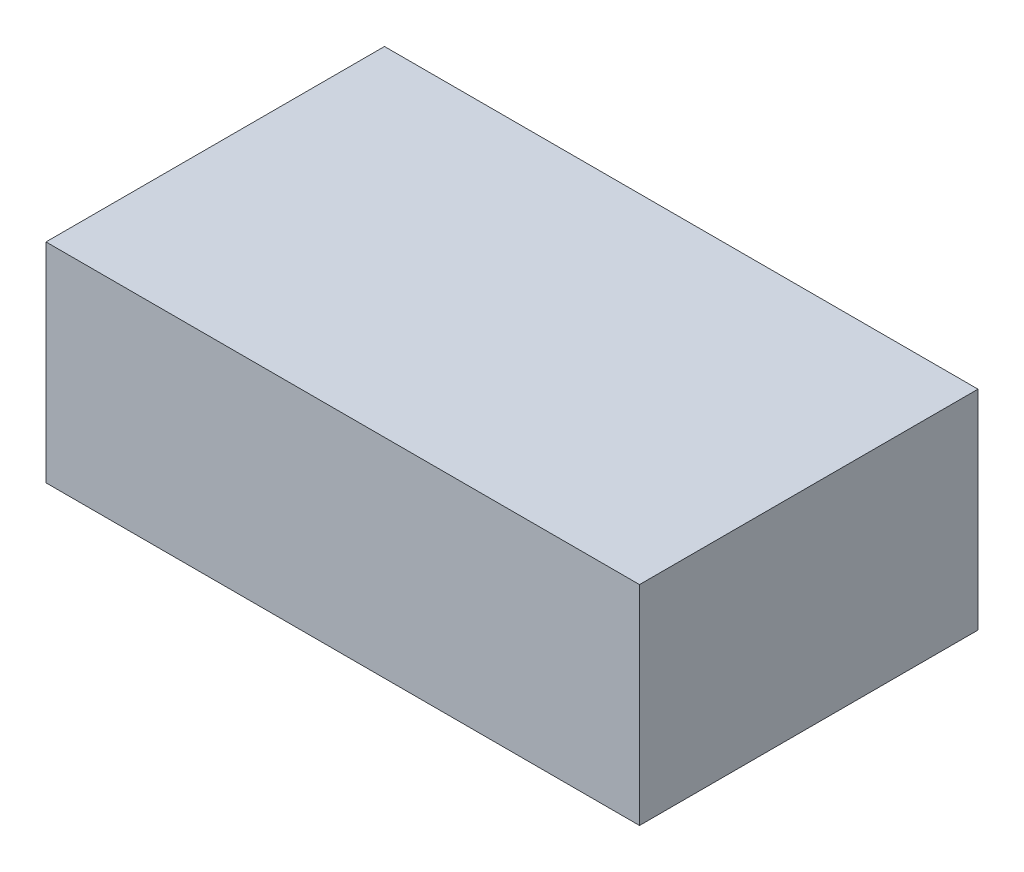
SolidWorks part; units mm, degrees
material "ABS"
ref_plane "Front Plane" through (0, 0, 0) normal (0, 0, 1) x (1, 0, 0)
ref_plane "Top Plane" through (0, 0, 0) normal (0, 1, 0) x (1, 0, 0)
ref_plane "Right Plane" through (0, 0, 0) normal (1, 0, 0) x (0, 0, -1)
sketch "Sketch6" plane through (0, 0, 0) normal (0, 1, 0) x (1, 0, 0)
  line L1 (64, 36.5) -> (-64, 36.5)
  line L2 (64, 36.5) -> (64, -36.5)
  line L3 (64, -36.5) -> (-64, -36.5)
  line L4 (-64, 36.5) -> (-64, -36.5)
  line L5 (64, 36.5) -> (-64, -36.5) construction
  line L6 (64, -36.5) -> (-64, 36.5) construction
  point P0 (0, 0)
  dimension "D1" = 128
  dimension "D2" = 73
extrude "Boss-Extrude1" add sketch "Sketch6" against normal blind 4
sketch "Sketch7" plane through (0, -4, 0) normal (0, -1, 0) x (1, 0, 0)
  line L0 (64, 36.5) -> (64, -36.5) construction
  line L1 (64, -36.5) -> (-64, -36.5) construction
  line L2 (-64, -36.5) -> (-64, 36.5) construction
  line L3 (-64, 36.5) -> (64, 36.5) construction
  line L4 (64, 36.5) -> (64, -36.5)
  line L5 (64, -36.5) -> (-64, -36.5)
  line L6 (-64, -36.5) -> (-64, 36.5)
  line L7 (-64, 36.5) -> (64, 36.5)
  line L8 (-60, 32.5) -> (60, 32.5)
  line L9 (60, 32.5) -> (60, -32.5)
  line L10 (60, -32.5) -> (-60, -32.5)
  line L11 (-60, -32.5) -> (-60, 32.5)
  dimension "D1" = 4
extrude "Boss-Extrude2" add sketch "Sketch7" along normal blind 41
sketch "Sketch9" plane through (0, -4, 0) normal (0, -1, 0) x (1, 0, 0)
  line L0 (-5, 32.5) -> (-5, -32.5)
  line L1 (60, 32.5) -> (-60, 32.5) construction
  line L2 (-60, -32.5) -> (60, -32.5) construction
  line L3 (-5, -32.5) -> (-18.5, -32.5)
  line L4 (-60, -32.5) -> (60, -32.5) construction
  line L5 (-18.5, -32.5) -> (-18.5, -21.3)
  line L6 (-18.5, -21.3) -> (-15, -21.3)
  line L7 (-15, -21.3) -> (-15, -26.3)
  line L8 (-15, -26.3) -> (-11, -26.3)
  line L9 (-11, -26.3) -> (-11, 26.3)
  line L10 (-11, 26.3) -> (-15, 26.3)
  line L11 (-15, 26.3) -> (-15, 21.3)
  line L12 (-15, 21.3) -> (-18.5, 21.3)
  line L13 (-18.5, 21.3) -> (-18.5, 32.5)
  line L14 (-18.5, 32.5) -> (-5, 32.5)
  line L15 (60, -32.5) -> (60, 32.5) construction
  point P18 (-10.9139, -23.7027)
  point P19 (-11.503, -25.5876)
  point P20 (-17.747, -17.6943)
  point P23 (-21.3198, 21.3)
  dimension "D1" = 65
  dimension "D2" = 6
  dimension "D3" = 4
  dimension "D4" = 5
  dimension "D5" = 11.2
  dimension "D6" = 13.5
extrude "Boss-Extrude4" add sketch "Sketch9" along normal blind 34 contours L14 L0 L3 L5 L6 L7 L8 L9 L10 L11 L12 L13
sketch "Sketch10" plane through (0, 0, -36.5) normal (0, 0, -1) x (-1, 0, 0)
  line L0 (64, -45) -> (64, 0) construction
  line L2 (-64, 0) -> (64, 0) construction
  circle A0 centre (44, -25) radius 10.16
  point P6 (85.5057, -87.6627)
  dimension "D1" = 20.32
  dimension "D2" = 20
  dimension "D3" = 25
extrude "Cut-Extrude1" cut sketch "Sketch10" against normal up to next
sketch "Sketch13" plane through (-64, 0, 0) normal (-1, 0, 0) x (0, 0, 1)
  line L0 (-12, -25) -> (12, -25) construction
  line L1 (-12, -21) -> (12, -21)
  line L2 (-12, -29) -> (12, -29)
  arc A0 (-12, -21) -> (-12, -29) centre (-12, -25) ccw
  arc A1 (12, -29) -> (12, -21) centre (12, -25) ccw
  point P2 (0, -25)
  point P7 (0, 0)
  dimension "D2" = 4
  dimension "D1" = 24
  dimension "D3" = 25
extrude "Cut-Extrude2" cut sketch "Sketch13" against normal up to next contours L2 A1 L1 A0
